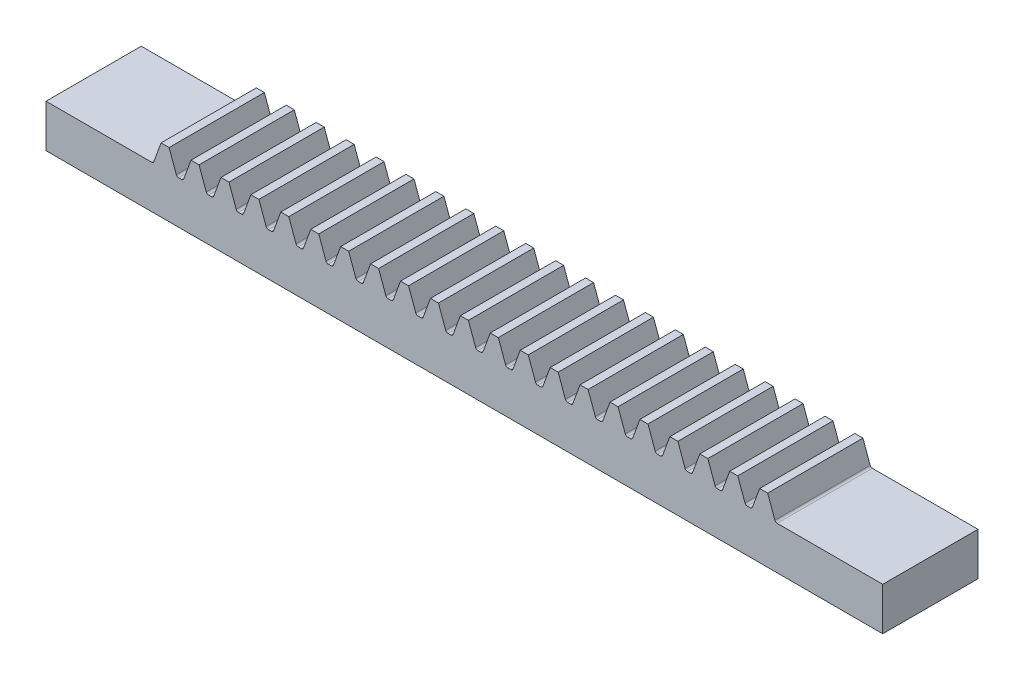
SolidWorks part; units mm, degrees
material "ABS"
ref_plane "Front Plane" through (0, 0, 0) normal (0, 0, 1) x (1, 0, 0)
ref_plane "Top Plane" through (0, 0, 0) normal (0, 1, 0) x (1, 0, 0)
ref_plane "Right Plane" through (0, 0, 0) normal (1, 0, 0) x (0, 0, -1)
sketch "Sketch1" plane through (0, 0, 0) normal (0, 0, 1) x (1, 0, 0)
  line L0 (5.5, 0) -> (-5.5, 0) construction
  line L1 (-77.8319, 4) -> (77.8319, 4)
  line L2 (-77.8319, 4) -> (-77.8319, 0)
  line L3 (-77.8319, 0) -> (77.8319, 0)
  line L4 (77.8319, 4) -> (77.8319, 0)
  line L5 (0, -9.2078) -> (0, 9.2078) construction
  dimension "D1" = 155.6637
  dimension "D2" = 77.8319
extrude "Boss-Extrude1" add sketch "Sketch1" along normal blind 10
sketch "Sketch2" plane through (0, 0, 0) normal (0, 0, 1) x (1, 0, 0)
  line L0 (-65.3126, 4) -> (-63.6747, 8.5)
  line L1 (77.8319, 4) -> (-77.8319, 4) construction
  line L2 (-63.6747, 8.5) -> (-61.989, 8.5)
  line L3 (-61.989, 8.5) -> (-60.3511, 4)
  line L4 (-65.3126, 4) -> (-60.3511, 4)
  line L5 (0, -9.2078) -> (0, 9.2078) construction
  line L6 (-62.8319, 8.5) -> (-62.8319, 4) construction
  line L9 (-34.7801, 6.5) -> (34.9733, 6.5) construction
  point P18 (-61.2611, 6.5)
  point P19 (-64.4026, 6.5)
  dimension "D2" = 20
  dimension "D3" = 40
  dimension "D4" = 62.8319
  dimension "D1" = 2.5
  dimension "D5" = 2
  dimension "D6" = 3.1416
extrude "Boss-Extrude4" add sketch "Sketch2" along normal up to surface (10 mm away) up to face at (0, 2, 10)
fillet "Fillet1" radius 0.5 2 edges
pattern_linear "LPattern1" count 21 spacing 6.2832 along (1, 0, 0) of "Boss-Extrude4", "Fillet1"
hole_wizard "CSK for M4 Hex Socket Countersunk Cap Screw1" [suppressed] positions "Sketch7" profile "Sketch6" countersink size "M4" standard "ISO"
sketch "Sketch7" plane through (0, 4, 0) normal (0, 1, 0) x (1, 0, 0)
  line L0 (-77.8319, -10) -> (-77.8319, 0) construction
  line L1 (77.8319, -10) -> (77.8319, 0) construction
  line L2 (-4.5728, 0) -> (4.5728, 0) construction
  point P0 (-71.8319, -5)
  point P2 (71.8319, -5)
  dimension "D1" = 6
  dimension "D2" = 6
  dimension "D3" = 5
  dimension "D4" = 5
sketch "Sketch6" plane through (-71.8319, 4, 5) normal (1, 0, 0) x (0, 0, 1)
  line L0 (0, 0) -> (0, 4)
  line L1 (0, 4) -> (2.25, 4)
  line L2 (2.25, 4) -> (2.25, 2.23)
  line L3 (2.25, 2.23) -> (4.48, 0)
  line L5 (4.48, 0) -> (0, 0)
  line L6 (-2.25, 2.23) -> (-4.48, 0) construction
  line L11 (0, -6.35) -> (0, 107.95) construction
  dimension "Thru Hole Dia." = 4.5
  dimension "Thru Hole Depth" = 4
  dimension "Near C'Sink Dia." = 8.96
  dimension "Near C'Sink Angle" = 90
ref_plane "Plane1" through (0, 26.5, 0) normal (0, 1, 0) x (1, 0, 0)
sketch "Sketch8" [suppressed] plane through (0, 0, 0) normal (0, -1, 0) x (1, 0, 0)
  line L4 (-77.8319, 0) -> (77.8319, 0)
  line L5 (77.8319, 0) -> (77.8319, 10)
  line L6 (77.8319, 10) -> (-77.8319, 10)
  line L7 (-77.8319, 10) -> (-77.8319, 0)
  line L8 (-77.8319, 0) -> (77.8319, 0)
  line L9 (77.8319, 0) -> (77.8319, 10)
  line L10 (77.8319, 10) -> (-77.8319, 10)
  line L11 (-77.8319, 10) -> (-77.8319, 0)
  circle A0 centre (-71.8319, 5) radius 2.25 construction
  circle A1 centre (-71.8319, 5) radius 2.25
  dimension "D1" = 0
extrude "Boss-Extrude5" [suppressed] add sketch "Sketch8" along normal blind 30
sketch "Sketch9" plane through (0, 0, 10) normal (0, 0, 1) x (1, 0, 0)
  line L88 (-77.8319, 4) -> (-77.8319, 0)
  line L89 (-77.8319, 0) -> (77.8319, 0)
  line L90 (-77.8319, 4) -> (-77.8319, 0)
  line L91 (77.8319, 4) -> (65.6627, 4)
  line L92 (65.1928, 4.329) -> (63.6747, 8.5)
  line L93 (63.6747, 8.5) -> (61.989, 8.5)
  line L94 (61.989, 8.5) -> (60.4709, 4.329)
  line L95 (60.001, 4) -> (59.3795, 4)
  line L96 (58.9096, 4.329) -> (57.3915, 8.5)
  line L97 (57.3915, 8.5) -> (55.7058, 8.5)
  line L98 (55.7058, 8.5) -> (54.1877, 4.329)
  line L99 (53.7178, 4) -> (53.0963, 4)
  line L100 (52.6265, 4.329) -> (51.1083, 8.5)
  line L101 (51.1083, 8.5) -> (49.4226, 8.5)
  line L102 (49.4226, 8.5) -> (47.9045, 4.329)
  line L103 (47.4347, 4) -> (46.8131, 4)
  line L104 (46.3433, 4.329) -> (44.8252, 8.5)
  line L105 (44.8252, 8.5) -> (43.1394, 8.5)
  line L106 (43.1394, 8.5) -> (41.6213, 4.329)
  line L107 (41.1515, 4) -> (40.5299, 4)
  line L108 (40.0601, 4.329) -> (38.542, 8.5)
  line L109 (38.542, 8.5) -> (36.8563, 8.5)
  line L110 (36.8563, 8.5) -> (35.3381, 4.329)
  line L111 (34.8683, 4) -> (34.2468, 4)
  line L112 (33.7769, 4.329) -> (32.2588, 8.5)
  line L113 (32.2588, 8.5) -> (30.5731, 8.5)
  line L114 (30.5731, 8.5) -> (29.0549, 4.329)
  line L115 (28.5851, 4) -> (27.9636, 4)
  line L116 (27.4937, 4.329) -> (25.9756, 8.5)
  line L117 (25.9756, 8.5) -> (24.2899, 8.5)
  line L118 (24.2899, 8.5) -> (22.7718, 4.329)
  line L119 (22.3019, 4) -> (21.6804, 4)
  line L120 (21.2105, 4.329) -> (19.6924, 8.5)
  line L121 (19.6924, 8.5) -> (18.0067, 8.5)
  line L122 (18.0067, 8.5) -> (16.4886, 4.329)
  line L123 (16.0187, 4) -> (15.3972, 4)
  line L124 (14.9273, 4.329) -> (13.4092, 8.5)
  line L125 (13.4092, 8.5) -> (11.7235, 8.5)
  line L126 (11.7235, 8.5) -> (10.2054, 4.329)
  line L127 (9.7355, 4) -> (9.114, 4)
  line L128 (8.6442, 4.329) -> (7.126, 8.5)
  line L129 (7.126, 8.5) -> (5.4403, 8.5)
  line L130 (5.4403, 8.5) -> (3.9222, 4.329)
  line L131 (3.4524, 4) -> (2.8308, 4)
  line L132 (2.361, 4.329) -> (0.8429, 8.5)
  line L133 (0.8429, 8.5) -> (-0.8429, 8.5)
  line L134 (-0.8429, 8.5) -> (-2.361, 4.329)
  line L135 (-2.8308, 4) -> (-3.4524, 4)
  line L136 (-3.9222, 4.329) -> (-5.4403, 8.5)
  line L137 (-5.4403, 8.5) -> (-7.126, 8.5)
  line L138 (-7.126, 8.5) -> (-8.6442, 4.329)
  line L139 (-9.114, 4) -> (-9.7355, 4)
  line L140 (-10.2054, 4.329) -> (-11.7235, 8.5)
  line L141 (-11.7235, 8.5) -> (-13.4092, 8.5)
  line L142 (-13.4092, 8.5) -> (-14.9273, 4.329)
  line L143 (-15.3972, 4) -> (-16.0187, 4)
  line L144 (-16.4886, 4.329) -> (-18.0067, 8.5)
  line L145 (-18.0067, 8.5) -> (-19.6924, 8.5)
  line L146 (-19.6924, 8.5) -> (-21.2105, 4.329)
  line L147 (-21.6804, 4) -> (-22.3019, 4)
  line L148 (-22.7718, 4.329) -> (-24.2899, 8.5)
  line L149 (-24.2899, 8.5) -> (-25.9756, 8.5)
  line L150 (-25.9756, 8.5) -> (-27.4937, 4.329)
  line L151 (-27.9636, 4) -> (-28.5851, 4)
  line L152 (-29.0549, 4.329) -> (-30.5731, 8.5)
  line L153 (-30.5731, 8.5) -> (-32.2588, 8.5)
  line L154 (-32.2588, 8.5) -> (-33.7769, 4.329)
  line L155 (-34.2468, 4) -> (-34.8683, 4)
  line L156 (-35.3381, 4.329) -> (-36.8563, 8.5)
  line L157 (-36.8563, 8.5) -> (-38.542, 8.5)
  line L158 (-38.542, 8.5) -> (-40.0601, 4.329)
  line L159 (-40.5299, 4) -> (-41.1515, 4)
  line L160 (-41.6213, 4.329) -> (-43.1394, 8.5)
  line L161 (-43.1394, 8.5) -> (-44.8252, 8.5)
  line L162 (-44.8252, 8.5) -> (-46.3433, 4.329)
  line L163 (-46.8131, 4) -> (-47.4347, 4)
  line L164 (-47.9045, 4.329) -> (-49.4226, 8.5)
  line L165 (-49.4226, 8.5) -> (-51.1083, 8.5)
  line L166 (-51.1083, 8.5) -> (-52.6265, 4.329)
  line L167 (-53.0963, 4) -> (-53.7178, 4)
  line L168 (-54.1877, 4.329) -> (-55.7058, 8.5)
  line L169 (-55.7058, 8.5) -> (-57.3915, 8.5)
  line L170 (-57.3915, 8.5) -> (-58.9096, 4.329)
  line L171 (-59.3795, 4) -> (-60.001, 4)
  line L172 (-60.4709, 4.329) -> (-61.989, 8.5)
  line L173 (-61.989, 8.5) -> (-63.6747, 8.5)
  line L174 (-63.6747, 8.5) -> (-65.1928, 4.329)
  line L175 (-65.6627, 4) -> (-77.8319, 4)
  line L176 (77.8319, 0) -> (77.8319, 4)
  line L177 (-77.8319, 0) -> (77.8319, 0)
  line L178 (77.8319, 0) -> (77.8319, 4)
  line L179 (77.8319, 4) -> (65.6627, 4)
  line L180 (65.1928, 4.329) -> (63.6747, 8.5)
  line L181 (63.6747, 8.5) -> (61.989, 8.5)
  line L182 (61.989, 8.5) -> (60.4709, 4.329)
  line L183 (60.001, 4) -> (59.3795, 4)
  line L184 (58.9096, 4.329) -> (57.3915, 8.5)
  line L185 (57.3915, 8.5) -> (55.7058, 8.5)
  line L186 (55.7058, 8.5) -> (54.1877, 4.329)
  line L187 (53.7178, 4) -> (53.0963, 4)
  line L188 (52.6265, 4.329) -> (51.1083, 8.5)
  line L189 (51.1083, 8.5) -> (49.4226, 8.5)
  line L190 (49.4226, 8.5) -> (47.9045, 4.329)
  line L191 (47.4347, 4) -> (46.8131, 4)
  line L192 (46.3433, 4.329) -> (44.8252, 8.5)
  line L193 (44.8252, 8.5) -> (43.1394, 8.5)
  line L194 (43.1394, 8.5) -> (41.6213, 4.329)
  line L195 (41.1515, 4) -> (40.5299, 4)
  line L196 (40.0601, 4.329) -> (38.542, 8.5)
  line L197 (38.542, 8.5) -> (36.8563, 8.5)
  line L198 (36.8563, 8.5) -> (35.3381, 4.329)
  line L199 (34.8683, 4) -> (34.2468, 4)
  line L200 (33.7769, 4.329) -> (32.2588, 8.5)
  line L201 (32.2588, 8.5) -> (30.5731, 8.5)
  line L202 (30.5731, 8.5) -> (29.0549, 4.329)
  line L203 (28.5851, 4) -> (27.9636, 4)
  line L204 (27.4937, 4.329) -> (25.9756, 8.5)
  line L205 (25.9756, 8.5) -> (24.2899, 8.5)
  line L206 (24.2899, 8.5) -> (22.7718, 4.329)
  line L207 (22.3019, 4) -> (21.6804, 4)
  line L208 (21.2105, 4.329) -> (19.6924, 8.5)
  line L209 (19.6924, 8.5) -> (18.0067, 8.5)
  line L210 (18.0067, 8.5) -> (16.4886, 4.329)
  line L211 (16.0187, 4) -> (15.3972, 4)
  line L212 (14.9273, 4.329) -> (13.4092, 8.5)
  line L213 (13.4092, 8.5) -> (11.7235, 8.5)
  line L214 (11.7235, 8.5) -> (10.2054, 4.329)
  line L215 (9.7355, 4) -> (9.114, 4)
  line L216 (8.6442, 4.329) -> (7.126, 8.5)
  line L217 (7.126, 8.5) -> (5.4403, 8.5)
  line L218 (5.4403, 8.5) -> (3.9222, 4.329)
  line L219 (3.4524, 4) -> (2.8308, 4)
  line L220 (2.361, 4.329) -> (0.8429, 8.5)
  line L221 (0.8429, 8.5) -> (-0.8429, 8.5)
  line L222 (-0.8429, 8.5) -> (-2.361, 4.329)
  line L223 (-2.8308, 4) -> (-3.4524, 4)
  line L224 (-3.9222, 4.329) -> (-5.4403, 8.5)
  line L225 (-5.4403, 8.5) -> (-7.126, 8.5)
  line L226 (-7.126, 8.5) -> (-8.6442, 4.329)
  line L227 (-9.114, 4) -> (-9.7355, 4)
  line L228 (-10.2054, 4.329) -> (-11.7235, 8.5)
  line L229 (-11.7235, 8.5) -> (-13.4092, 8.5)
  line L230 (-13.4092, 8.5) -> (-14.9273, 4.329)
  line L231 (-15.3972, 4) -> (-16.0187, 4)
  line L232 (-16.4886, 4.329) -> (-18.0067, 8.5)
  line L233 (-18.0067, 8.5) -> (-19.6924, 8.5)
  line L234 (-19.6924, 8.5) -> (-21.2105, 4.329)
  line L235 (-21.6804, 4) -> (-22.3019, 4)
  line L236 (-22.7718, 4.329) -> (-24.2899, 8.5)
  line L237 (-24.2899, 8.5) -> (-25.9756, 8.5)
  line L238 (-25.9756, 8.5) -> (-27.4937, 4.329)
  line L239 (-27.9636, 4) -> (-28.5851, 4)
  line L240 (-29.0549, 4.329) -> (-30.5731, 8.5)
  line L241 (-30.5731, 8.5) -> (-32.2588, 8.5)
  line L242 (-32.2588, 8.5) -> (-33.7769, 4.329)
  line L243 (-34.2468, 4) -> (-34.8683, 4)
  line L244 (-35.3381, 4.329) -> (-36.8563, 8.5)
  line L245 (-36.8563, 8.5) -> (-38.542, 8.5)
  line L246 (-38.542, 8.5) -> (-40.0601, 4.329)
  line L247 (-40.5299, 4) -> (-41.1515, 4)
  line L248 (-41.6213, 4.329) -> (-43.1394, 8.5)
  line L249 (-43.1394, 8.5) -> (-44.8252, 8.5)
  line L250 (-44.8252, 8.5) -> (-46.3433, 4.329)
  line L251 (-46.8131, 4) -> (-47.4347, 4)
  line L252 (-47.9045, 4.329) -> (-49.4226, 8.5)
  line L253 (-49.4226, 8.5) -> (-51.1083, 8.5)
  line L254 (-51.1083, 8.5) -> (-52.6265, 4.329)
  line L255 (-53.0963, 4) -> (-53.7178, 4)
  line L256 (-54.1877, 4.329) -> (-55.7058, 8.5)
  line L257 (-55.7058, 8.5) -> (-57.3915, 8.5)
  line L258 (-57.3915, 8.5) -> (-58.9096, 4.329)
  line L259 (-59.3795, 4) -> (-60.001, 4)
  line L260 (-60.4709, 4.329) -> (-61.989, 8.5)
  line L261 (-61.989, 8.5) -> (-63.6747, 8.5)
  line L262 (-63.6747, 8.5) -> (-65.1928, 4.329)
  line L263 (-65.6627, 4) -> (-77.8319, 4)
  arc A42 (65.1928, 4.329) -> (65.6627, 4) centre (65.6627, 4.5) ccw
  arc A43 (60.001, 4) -> (60.4709, 4.329) centre (60.001, 4.5) ccw
  arc A44 (58.9096, 4.329) -> (59.3795, 4) centre (59.3795, 4.5) ccw
  arc A45 (53.7178, 4) -> (54.1877, 4.329) centre (53.7178, 4.5) ccw
  arc A46 (52.6265, 4.329) -> (53.0963, 4) centre (53.0963, 4.5) ccw
  arc A47 (47.4347, 4) -> (47.9045, 4.329) centre (47.4347, 4.5) ccw
  arc A48 (46.3433, 4.329) -> (46.8131, 4) centre (46.8131, 4.5) ccw
  arc A49 (41.1515, 4) -> (41.6213, 4.329) centre (41.1515, 4.5) ccw
  arc A50 (40.0601, 4.329) -> (40.5299, 4) centre (40.5299, 4.5) ccw
  arc A51 (34.8683, 4) -> (35.3381, 4.329) centre (34.8683, 4.5) ccw
  arc A52 (33.7769, 4.329) -> (34.2468, 4) centre (34.2468, 4.5) ccw
  arc A53 (28.5851, 4) -> (29.0549, 4.329) centre (28.5851, 4.5) ccw
  arc A54 (27.4937, 4.329) -> (27.9636, 4) centre (27.9636, 4.5) ccw
  arc A55 (22.3019, 4) -> (22.7718, 4.329) centre (22.3019, 4.5) ccw
  arc A56 (21.2105, 4.329) -> (21.6804, 4) centre (21.6804, 4.5) ccw
  arc A57 (16.0187, 4) -> (16.4886, 4.329) centre (16.0187, 4.5) ccw
  arc A58 (14.9273, 4.329) -> (15.3972, 4) centre (15.3972, 4.5) ccw
  arc A59 (9.7355, 4) -> (10.2054, 4.329) centre (9.7355, 4.5) ccw
  arc A60 (8.6442, 4.329) -> (9.114, 4) centre (9.114, 4.5) ccw
  arc A61 (3.4524, 4) -> (3.9222, 4.329) centre (3.4524, 4.5) ccw
  arc A62 (2.361, 4.329) -> (2.8308, 4) centre (2.8308, 4.5) ccw
  arc A63 (-2.8308, 4) -> (-2.361, 4.329) centre (-2.8308, 4.5) ccw
  arc A64 (-3.9222, 4.329) -> (-3.4524, 4) centre (-3.4524, 4.5) ccw
  arc A65 (-9.114, 4) -> (-8.6442, 4.329) centre (-9.114, 4.5) ccw
  arc A66 (-10.2054, 4.329) -> (-9.7355, 4) centre (-9.7355, 4.5) ccw
  arc A67 (-15.3972, 4) -> (-14.9273, 4.329) centre (-15.3972, 4.5) ccw
  arc A68 (-16.4886, 4.329) -> (-16.0187, 4) centre (-16.0187, 4.5) ccw
  arc A69 (-21.6804, 4) -> (-21.2105, 4.329) centre (-21.6804, 4.5) ccw
  arc A70 (-22.7718, 4.329) -> (-22.3019, 4) centre (-22.3019, 4.5) ccw
  arc A71 (-27.9636, 4) -> (-27.4937, 4.329) centre (-27.9636, 4.5) ccw
  arc A72 (-29.0549, 4.329) -> (-28.5851, 4) centre (-28.5851, 4.5) ccw
  arc A73 (-34.2468, 4) -> (-33.7769, 4.329) centre (-34.2468, 4.5) ccw
  arc A74 (-35.3381, 4.329) -> (-34.8683, 4) centre (-34.8683, 4.5) ccw
  arc A75 (-40.5299, 4) -> (-40.0601, 4.329) centre (-40.5299, 4.5) ccw
  arc A76 (-41.6213, 4.329) -> (-41.1515, 4) centre (-41.1515, 4.5) ccw
  arc A77 (-46.8131, 4) -> (-46.3433, 4.329) centre (-46.8131, 4.5) ccw
  arc A78 (-47.9045, 4.329) -> (-47.4347, 4) centre (-47.4347, 4.5) ccw
  arc A79 (-53.0963, 4) -> (-52.6265, 4.329) centre (-53.0963, 4.5) ccw
  arc A80 (-54.1877, 4.329) -> (-53.7178, 4) centre (-53.7178, 4.5) ccw
  arc A81 (-59.3795, 4) -> (-58.9096, 4.329) centre (-59.3795, 4.5) ccw
  arc A82 (-60.4709, 4.329) -> (-60.001, 4) centre (-60.001, 4.5) ccw
  arc A83 (-65.6627, 4) -> (-65.1928, 4.329) centre (-65.6627, 4.5) ccw
  arc A84 (65.1928, 4.329) -> (65.6627, 4) centre (65.6627, 4.5) ccw
  arc A85 (60.001, 4) -> (60.4709, 4.329) centre (60.001, 4.5) ccw
  arc A86 (58.9096, 4.329) -> (59.3795, 4) centre (59.3795, 4.5) ccw
  arc A87 (53.7178, 4) -> (54.1877, 4.329) centre (53.7178, 4.5) ccw
  arc A88 (52.6265, 4.329) -> (53.0963, 4) centre (53.0963, 4.5) ccw
  arc A89 (47.4347, 4) -> (47.9045, 4.329) centre (47.4347, 4.5) ccw
  arc A90 (46.3433, 4.329) -> (46.8131, 4) centre (46.8131, 4.5) ccw
  arc A91 (41.1515, 4) -> (41.6213, 4.329) centre (41.1515, 4.5) ccw
  arc A92 (40.0601, 4.329) -> (40.5299, 4) centre (40.5299, 4.5) ccw
  arc A93 (34.8683, 4) -> (35.3381, 4.329) centre (34.8683, 4.5) ccw
  arc A94 (33.7769, 4.329) -> (34.2468, 4) centre (34.2468, 4.5) ccw
  arc A95 (28.5851, 4) -> (29.0549, 4.329) centre (28.5851, 4.5) ccw
  arc A96 (27.4937, 4.329) -> (27.9636, 4) centre (27.9636, 4.5) ccw
  arc A97 (22.3019, 4) -> (22.7718, 4.329) centre (22.3019, 4.5) ccw
  arc A98 (21.2105, 4.329) -> (21.6804, 4) centre (21.6804, 4.5) ccw
  arc A99 (16.0187, 4) -> (16.4886, 4.329) centre (16.0187, 4.5) ccw
  arc A100 (14.9273, 4.329) -> (15.3972, 4) centre (15.3972, 4.5) ccw
  arc A101 (9.7355, 4) -> (10.2054, 4.329) centre (9.7355, 4.5) ccw
  arc A102 (8.6442, 4.329) -> (9.114, 4) centre (9.114, 4.5) ccw
  arc A103 (3.4524, 4) -> (3.9222, 4.329) centre (3.4524, 4.5) ccw
  arc A104 (2.361, 4.329) -> (2.8308, 4) centre (2.8308, 4.5) ccw
  arc A105 (-2.8308, 4) -> (-2.361, 4.329) centre (-2.8308, 4.5) ccw
  arc A106 (-3.9222, 4.329) -> (-3.4524, 4) centre (-3.4524, 4.5) ccw
  arc A107 (-9.114, 4) -> (-8.6442, 4.329) centre (-9.114, 4.5) ccw
  arc A108 (-10.2054, 4.329) -> (-9.7355, 4) centre (-9.7355, 4.5) ccw
  arc A109 (-15.3972, 4) -> (-14.9273, 4.329) centre (-15.3972, 4.5) ccw
  arc A110 (-16.4886, 4.329) -> (-16.0187, 4) centre (-16.0187, 4.5) ccw
  arc A111 (-21.6804, 4) -> (-21.2105, 4.329) centre (-21.6804, 4.5) ccw
  arc A112 (-22.7718, 4.329) -> (-22.3019, 4) centre (-22.3019, 4.5) ccw
  arc A113 (-27.9636, 4) -> (-27.4937, 4.329) centre (-27.9636, 4.5) ccw
  arc A114 (-29.0549, 4.329) -> (-28.5851, 4) centre (-28.5851, 4.5) ccw
  arc A115 (-34.2468, 4) -> (-33.7769, 4.329) centre (-34.2468, 4.5) ccw
  arc A116 (-35.3381, 4.329) -> (-34.8683, 4) centre (-34.8683, 4.5) ccw
  arc A117 (-40.5299, 4) -> (-40.0601, 4.329) centre (-40.5299, 4.5) ccw
  arc A118 (-41.6213, 4.329) -> (-41.1515, 4) centre (-41.1515, 4.5) ccw
  arc A119 (-46.8131, 4) -> (-46.3433, 4.329) centre (-46.8131, 4.5) ccw
  arc A120 (-47.9045, 4.329) -> (-47.4347, 4) centre (-47.4347, 4.5) ccw
  arc A121 (-53.0963, 4) -> (-52.6265, 4.329) centre (-53.0963, 4.5) ccw
  arc A122 (-54.1877, 4.329) -> (-53.7178, 4) centre (-53.7178, 4.5) ccw
  arc A123 (-59.3795, 4) -> (-58.9096, 4.329) centre (-59.3795, 4.5) ccw
  arc A124 (-60.4709, 4.329) -> (-60.001, 4) centre (-60.001, 4.5) ccw
  arc A125 (-65.6627, 4) -> (-65.1928, 4.329) centre (-65.6627, 4.5) ccw
  dimension "D1" = 0
extrude "Boss-Extrude6" add sketch "Sketch9" along normal blind 6 contours L262 A125 L263 L90 L177 L178 L179 A84 L180 L181 L182 A85 L183 A86 L184 L185 L186 A87 L187 A88 L188 L189 L190 A89 L191 A90 L192 L193 L194 A91 L195 A92 L196 L197 L198 A93 L199 A94 L200 L201 L202 A95 L203 A96 L204 L205 L206 A97 L207 A98 L208 L209 L210 A99 L211 A100 L212 L213 L214 A101 L215 A102 L216 L217 L218 A103 L219 A104 L220 L221 L222 A105 L223 A106 L224 L225 L226 A107 L227 A108 L228 L229 L230 A109 L231 A110 L232 L233 L234 A111 L235 A112 L236 L237 L238 A113 L239 A114 L240 L241 L242 A115 L243 A116 L244 L245 L246 A117 L247 A118 L248 L249 L250 A119 L251 A120 L252 L253 L254 A121 L255 A122 L256 L257 L258 A123 L259 A124 L260 L261
sketch "Sketch10" [suppressed] plane through (0, 0, 16) normal (0, 0, 1) x (1, 0, 0)
  line L0 (-49.4226, 8.5) -> (-51.1083, 8.5) construction
  line L1 (-77.8319, -30) -> (90.1846, -30)
  line L2 (-77.8319, -30) -> (-77.8319, -7.5)
  line L3 (-77.8319, -7.5) -> (90.1846, -7.5)
  line L4 (90.1846, -30) -> (90.1846, -7.5)
  dimension "D1" = 16
extrude "Cut-Extrude1" [suppressed] cut sketch "Sketch10" against normal blind 40
sketch "Sketch11" plane through (-77.8319, 0, 0) normal (-1, 0, 0) x (0, 0, 1)
  line L4 (0, 4) -> (0, 0)
  line L5 (0, 0) -> (16, 0)
  line L6 (16, 0) -> (16, 4)
  line L7 (16, 4) -> (0, 4)
  line L8 (0, 4) -> (0, 0)
  line L9 (0, 0) -> (16, 0)
  line L10 (16, 0) -> (16, 4)
  line L11 (16, 4) -> (0, 4)
  dimension "D1" = 0
extrude "Boss-Extrude8" add sketch "Sketch11" along normal blind 10
sketch "Sketch12" plane through (77.8319, 0, 0) normal (1, 0, 0) x (0, 0, -1)
  line L4 (-16, 4) -> (-16, 0)
  line L5 (-16, 0) -> (0, 0)
  line L6 (0, 0) -> (0, 4)
  line L7 (0, 4) -> (-16, 4)
  line L8 (-16, 4) -> (-16, 0)
  line L9 (-16, 0) -> (0, 0)
  line L10 (0, 0) -> (0, 4)
  line L11 (0, 4) -> (-16, 4)
  dimension "D1" = 0
extrude "Boss-Extrude9" add sketch "Sketch12" along normal blind 10
sketch "Sketch15" plane through (0, 0, 0) normal (0, -1, 0) x (1, 0, 0)
  line L4 (-87.8319, 0) -> (87.8319, 0)
  line L5 (87.8319, 0) -> (87.8319, 16)
  line L6 (87.8319, 16) -> (-87.8319, 16)
  line L7 (-87.8319, 16) -> (-87.8319, 0)
  line L8 (-87.8319, 0) -> (87.8319, 0)
  line L9 (87.8319, 0) -> (87.8319, 16)
  line L10 (87.8319, 16) -> (-87.8319, 16)
  line L11 (-87.8319, 16) -> (-87.8319, 0)
  dimension "D1" = 0
extrude "Boss-Extrude10" add sketch "Sketch15" along normal blind 5
sketch "Sketch16" plane through (0, 0, 16) normal (0, 0, 1) x (1, 0, 0)
  line L88 (-61.989, 8.5) -> (-63.6747, 8.5)
  line L89 (-63.6747, 8.5) -> (-65.1928, 4.329)
  line L90 (-65.6627, 4) -> (-87.8319, 4)
  line L91 (-87.8319, 4) -> (-87.8319, -5)
  line L92 (-87.8319, -5) -> (87.8319, -5)
  line L93 (87.8319, -5) -> (87.8319, 4)
  line L94 (87.8319, 4) -> (65.6627, 4)
  line L95 (65.1928, 4.329) -> (63.6747, 8.5)
  line L96 (63.6747, 8.5) -> (61.989, 8.5)
  line L97 (61.989, 8.5) -> (60.4709, 4.329)
  line L98 (60.001, 4) -> (59.3795, 4)
  line L99 (58.9096, 4.329) -> (57.3915, 8.5)
  line L100 (57.3915, 8.5) -> (55.7058, 8.5)
  line L101 (55.7058, 8.5) -> (54.1877, 4.329)
  line L102 (53.7178, 4) -> (53.0963, 4)
  line L103 (52.6265, 4.329) -> (51.1083, 8.5)
  line L104 (51.1083, 8.5) -> (49.4226, 8.5)
  line L105 (49.4226, 8.5) -> (47.9045, 4.329)
  line L106 (47.4347, 4) -> (46.8131, 4)
  line L107 (46.3433, 4.329) -> (44.8252, 8.5)
  line L108 (44.8252, 8.5) -> (43.1394, 8.5)
  line L109 (43.1394, 8.5) -> (41.6213, 4.329)
  line L110 (41.1515, 4) -> (40.5299, 4)
  line L111 (40.0601, 4.329) -> (38.542, 8.5)
  line L112 (38.542, 8.5) -> (36.8563, 8.5)
  line L113 (36.8563, 8.5) -> (35.3381, 4.329)
  line L114 (34.8683, 4) -> (34.2468, 4)
  line L115 (33.7769, 4.329) -> (32.2588, 8.5)
  line L116 (32.2588, 8.5) -> (30.5731, 8.5)
  line L117 (30.5731, 8.5) -> (29.0549, 4.329)
  line L118 (28.5851, 4) -> (27.9636, 4)
  line L119 (27.4937, 4.329) -> (25.9756, 8.5)
  line L120 (25.9756, 8.5) -> (24.2899, 8.5)
  line L121 (24.2899, 8.5) -> (22.7718, 4.329)
  line L122 (22.3019, 4) -> (21.6804, 4)
  line L123 (21.2105, 4.329) -> (19.6924, 8.5)
  line L124 (19.6924, 8.5) -> (18.0067, 8.5)
  line L125 (18.0067, 8.5) -> (16.4886, 4.329)
  line L126 (16.0187, 4) -> (15.3972, 4)
  line L127 (14.9273, 4.329) -> (13.4092, 8.5)
  line L128 (13.4092, 8.5) -> (11.7235, 8.5)
  line L129 (11.7235, 8.5) -> (10.2054, 4.329)
  line L130 (9.7355, 4) -> (9.114, 4)
  line L131 (8.6442, 4.329) -> (7.126, 8.5)
  line L132 (7.126, 8.5) -> (5.4403, 8.5)
  line L133 (5.4403, 8.5) -> (3.9222, 4.329)
  line L134 (3.4524, 4) -> (2.8308, 4)
  line L135 (2.361, 4.329) -> (0.8429, 8.5)
  line L136 (0.8429, 8.5) -> (-0.8429, 8.5)
  line L137 (-0.8429, 8.5) -> (-2.361, 4.329)
  line L138 (-2.8308, 4) -> (-3.4524, 4)
  line L139 (-3.9222, 4.329) -> (-5.4403, 8.5)
  line L140 (-5.4403, 8.5) -> (-7.126, 8.5)
  line L141 (-7.126, 8.5) -> (-8.6442, 4.329)
  line L142 (-9.114, 4) -> (-9.7355, 4)
  line L143 (-10.2054, 4.329) -> (-11.7235, 8.5)
  line L144 (-11.7235, 8.5) -> (-13.4092, 8.5)
  line L145 (-13.4092, 8.5) -> (-14.9273, 4.329)
  line L146 (-15.3972, 4) -> (-16.0187, 4)
  line L147 (-16.4886, 4.329) -> (-18.0067, 8.5)
  line L148 (-18.0067, 8.5) -> (-19.6924, 8.5)
  line L149 (-19.6924, 8.5) -> (-21.2105, 4.329)
  line L150 (-21.6804, 4) -> (-22.3019, 4)
  line L151 (-22.7718, 4.329) -> (-24.2899, 8.5)
  line L152 (-24.2899, 8.5) -> (-25.9756, 8.5)
  line L153 (-25.9756, 8.5) -> (-27.4937, 4.329)
  line L154 (-27.9636, 4) -> (-28.5851, 4)
  line L155 (-29.0549, 4.329) -> (-30.5731, 8.5)
  line L156 (-30.5731, 8.5) -> (-32.2588, 8.5)
  line L157 (-32.2588, 8.5) -> (-33.7769, 4.329)
  line L158 (-34.2468, 4) -> (-34.8683, 4)
  line L159 (-35.3381, 4.329) -> (-36.8563, 8.5)
  line L160 (-36.8563, 8.5) -> (-38.542, 8.5)
  line L161 (-38.542, 8.5) -> (-40.0601, 4.329)
  line L162 (-40.5299, 4) -> (-41.1515, 4)
  line L163 (-41.6213, 4.329) -> (-43.1394, 8.5)
  line L164 (-43.1394, 8.5) -> (-44.8252, 8.5)
  line L165 (-44.8252, 8.5) -> (-46.3433, 4.329)
  line L166 (-46.8131, 4) -> (-47.4347, 4)
  line L167 (-47.9045, 4.329) -> (-49.4226, 8.5)
  line L168 (-49.4226, 8.5) -> (-51.1083, 8.5)
  line L169 (-51.1083, 8.5) -> (-52.6265, 4.329)
  line L170 (-53.0963, 4) -> (-53.7178, 4)
  line L171 (-54.1877, 4.329) -> (-55.7058, 8.5)
  line L172 (-55.7058, 8.5) -> (-57.3915, 8.5)
  line L173 (-57.3915, 8.5) -> (-58.9096, 4.329)
  line L174 (-59.3795, 4) -> (-60.001, 4)
  line L175 (-60.4709, 4.329) -> (-61.989, 8.5)
  line L176 (-61.989, 8.5) -> (-63.6747, 8.5)
  line L177 (-63.6747, 8.5) -> (-65.1928, 4.329)
  line L178 (-65.6627, 4) -> (-87.8319, 4)
  line L179 (-87.8319, 4) -> (-87.8319, -5)
  line L180 (-87.8319, -5) -> (87.8319, -5)
  line L181 (87.8319, -5) -> (87.8319, 4)
  line L182 (87.8319, 4) -> (65.6627, 4)
  line L183 (65.1928, 4.329) -> (63.6747, 8.5)
  line L184 (63.6747, 8.5) -> (61.989, 8.5)
  line L185 (61.989, 8.5) -> (60.4709, 4.329)
  line L186 (60.001, 4) -> (59.3795, 4)
  line L187 (58.9096, 4.329) -> (57.3915, 8.5)
  line L188 (57.3915, 8.5) -> (55.7058, 8.5)
  line L189 (55.7058, 8.5) -> (54.1877, 4.329)
  line L190 (53.7178, 4) -> (53.0963, 4)
  line L191 (52.6265, 4.329) -> (51.1083, 8.5)
  line L192 (51.1083, 8.5) -> (49.4226, 8.5)
  line L193 (49.4226, 8.5) -> (47.9045, 4.329)
  line L194 (47.4347, 4) -> (46.8131, 4)
  line L195 (46.3433, 4.329) -> (44.8252, 8.5)
  line L196 (44.8252, 8.5) -> (43.1394, 8.5)
  line L197 (43.1394, 8.5) -> (41.6213, 4.329)
  line L198 (41.1515, 4) -> (40.5299, 4)
  line L199 (40.0601, 4.329) -> (38.542, 8.5)
  line L200 (38.542, 8.5) -> (36.8563, 8.5)
  line L201 (36.8563, 8.5) -> (35.3381, 4.329)
  line L202 (34.8683, 4) -> (34.2468, 4)
  line L203 (33.7769, 4.329) -> (32.2588, 8.5)
  line L204 (32.2588, 8.5) -> (30.5731, 8.5)
  line L205 (30.5731, 8.5) -> (29.0549, 4.329)
  line L206 (28.5851, 4) -> (27.9636, 4)
  line L207 (27.4937, 4.329) -> (25.9756, 8.5)
  line L208 (25.9756, 8.5) -> (24.2899, 8.5)
  line L209 (24.2899, 8.5) -> (22.7718, 4.329)
  line L210 (22.3019, 4) -> (21.6804, 4)
  line L211 (21.2105, 4.329) -> (19.6924, 8.5)
  line L212 (19.6924, 8.5) -> (18.0067, 8.5)
  line L213 (18.0067, 8.5) -> (16.4886, 4.329)
  line L214 (16.0187, 4) -> (15.3972, 4)
  line L215 (14.9273, 4.329) -> (13.4092, 8.5)
  line L216 (13.4092, 8.5) -> (11.7235, 8.5)
  line L217 (11.7235, 8.5) -> (10.2054, 4.329)
  line L218 (9.7355, 4) -> (9.114, 4)
  line L219 (8.6442, 4.329) -> (7.126, 8.5)
  line L220 (7.126, 8.5) -> (5.4403, 8.5)
  line L221 (5.4403, 8.5) -> (3.9222, 4.329)
  line L222 (3.4524, 4) -> (2.8308, 4)
  line L223 (2.361, 4.329) -> (0.8429, 8.5)
  line L224 (0.8429, 8.5) -> (-0.8429, 8.5)
  line L225 (-0.8429, 8.5) -> (-2.361, 4.329)
  line L226 (-2.8308, 4) -> (-3.4524, 4)
  line L227 (-3.9222, 4.329) -> (-5.4403, 8.5)
  line L228 (-5.4403, 8.5) -> (-7.126, 8.5)
  line L229 (-7.126, 8.5) -> (-8.6442, 4.329)
  line L230 (-9.114, 4) -> (-9.7355, 4)
  line L231 (-10.2054, 4.329) -> (-11.7235, 8.5)
  line L232 (-11.7235, 8.5) -> (-13.4092, 8.5)
  line L233 (-13.4092, 8.5) -> (-14.9273, 4.329)
  line L234 (-15.3972, 4) -> (-16.0187, 4)
  line L235 (-16.4886, 4.329) -> (-18.0067, 8.5)
  line L236 (-18.0067, 8.5) -> (-19.6924, 8.5)
  line L237 (-19.6924, 8.5) -> (-21.2105, 4.329)
  line L238 (-21.6804, 4) -> (-22.3019, 4)
  line L239 (-22.7718, 4.329) -> (-24.2899, 8.5)
  line L240 (-24.2899, 8.5) -> (-25.9756, 8.5)
  line L241 (-25.9756, 8.5) -> (-27.4937, 4.329)
  line L242 (-27.9636, 4) -> (-28.5851, 4)
  line L243 (-29.0549, 4.329) -> (-30.5731, 8.5)
  line L244 (-30.5731, 8.5) -> (-32.2588, 8.5)
  line L245 (-32.2588, 8.5) -> (-33.7769, 4.329)
  line L246 (-34.2468, 4) -> (-34.8683, 4)
  line L247 (-35.3381, 4.329) -> (-36.8563, 8.5)
  line L248 (-36.8563, 8.5) -> (-38.542, 8.5)
  line L249 (-38.542, 8.5) -> (-40.0601, 4.329)
  line L250 (-40.5299, 4) -> (-41.1515, 4)
  line L251 (-41.6213, 4.329) -> (-43.1394, 8.5)
  line L252 (-43.1394, 8.5) -> (-44.8252, 8.5)
  line L253 (-44.8252, 8.5) -> (-46.3433, 4.329)
  line L254 (-46.8131, 4) -> (-47.4347, 4)
  line L255 (-47.9045, 4.329) -> (-49.4226, 8.5)
  line L256 (-49.4226, 8.5) -> (-51.1083, 8.5)
  line L257 (-51.1083, 8.5) -> (-52.6265, 4.329)
  line L258 (-53.0963, 4) -> (-53.7178, 4)
  line L259 (-54.1877, 4.329) -> (-55.7058, 8.5)
  line L260 (-55.7058, 8.5) -> (-57.3915, 8.5)
  line L261 (-57.3915, 8.5) -> (-58.9096, 4.329)
  line L262 (-59.3795, 4) -> (-60.001, 4)
  line L263 (-60.4709, 4.329) -> (-61.989, 8.5)
  arc A42 (-65.6627, 4) -> (-65.1928, 4.329) centre (-65.6627, 4.5) ccw
  arc A43 (65.1928, 4.329) -> (65.6627, 4) centre (65.6627, 4.5) ccw
  arc A44 (60.001, 4) -> (60.4709, 4.329) centre (60.001, 4.5) ccw
  arc A45 (58.9096, 4.329) -> (59.3795, 4) centre (59.3795, 4.5) ccw
  arc A46 (53.7178, 4) -> (54.1877, 4.329) centre (53.7178, 4.5) ccw
  arc A47 (52.6265, 4.329) -> (53.0963, 4) centre (53.0963, 4.5) ccw
  arc A48 (47.4347, 4) -> (47.9045, 4.329) centre (47.4347, 4.5) ccw
  arc A49 (46.3433, 4.329) -> (46.8131, 4) centre (46.8131, 4.5) ccw
  arc A50 (41.1515, 4) -> (41.6213, 4.329) centre (41.1515, 4.5) ccw
  arc A51 (40.0601, 4.329) -> (40.5299, 4) centre (40.5299, 4.5) ccw
  arc A52 (34.8683, 4) -> (35.3381, 4.329) centre (34.8683, 4.5) ccw
  arc A53 (33.7769, 4.329) -> (34.2468, 4) centre (34.2468, 4.5) ccw
  arc A54 (28.5851, 4) -> (29.0549, 4.329) centre (28.5851, 4.5) ccw
  arc A55 (27.4937, 4.329) -> (27.9636, 4) centre (27.9636, 4.5) ccw
  arc A56 (22.3019, 4) -> (22.7718, 4.329) centre (22.3019, 4.5) ccw
  arc A57 (21.2105, 4.329) -> (21.6804, 4) centre (21.6804, 4.5) ccw
  arc A58 (16.0187, 4) -> (16.4886, 4.329) centre (16.0187, 4.5) ccw
  arc A59 (14.9273, 4.329) -> (15.3972, 4) centre (15.3972, 4.5) ccw
  arc A60 (9.7355, 4) -> (10.2054, 4.329) centre (9.7355, 4.5) ccw
  arc A61 (8.6442, 4.329) -> (9.114, 4) centre (9.114, 4.5) ccw
  arc A62 (3.4524, 4) -> (3.9222, 4.329) centre (3.4524, 4.5) ccw
  arc A63 (2.361, 4.329) -> (2.8308, 4) centre (2.8308, 4.5) ccw
  arc A64 (-2.8308, 4) -> (-2.361, 4.329) centre (-2.8308, 4.5) ccw
  arc A65 (-3.9222, 4.329) -> (-3.4524, 4) centre (-3.4524, 4.5) ccw
  arc A66 (-9.114, 4) -> (-8.6442, 4.329) centre (-9.114, 4.5) ccw
  arc A67 (-10.2054, 4.329) -> (-9.7355, 4) centre (-9.7355, 4.5) ccw
  arc A68 (-15.3972, 4) -> (-14.9273, 4.329) centre (-15.3972, 4.5) ccw
  arc A69 (-16.4886, 4.329) -> (-16.0187, 4) centre (-16.0187, 4.5) ccw
  arc A70 (-21.6804, 4) -> (-21.2105, 4.329) centre (-21.6804, 4.5) ccw
  arc A71 (-22.7718, 4.329) -> (-22.3019, 4) centre (-22.3019, 4.5) ccw
  arc A72 (-27.9636, 4) -> (-27.4937, 4.329) centre (-27.9636, 4.5) ccw
  arc A73 (-29.0549, 4.329) -> (-28.5851, 4) centre (-28.5851, 4.5) ccw
  arc A74 (-34.2468, 4) -> (-33.7769, 4.329) centre (-34.2468, 4.5) ccw
  arc A75 (-35.3381, 4.329) -> (-34.8683, 4) centre (-34.8683, 4.5) ccw
  arc A76 (-40.5299, 4) -> (-40.0601, 4.329) centre (-40.5299, 4.5) ccw
  arc A77 (-41.6213, 4.329) -> (-41.1515, 4) centre (-41.1515, 4.5) ccw
  arc A78 (-46.8131, 4) -> (-46.3433, 4.329) centre (-46.8131, 4.5) ccw
  arc A79 (-47.9045, 4.329) -> (-47.4347, 4) centre (-47.4347, 4.5) ccw
  arc A80 (-53.0963, 4) -> (-52.6265, 4.329) centre (-53.0963, 4.5) ccw
  arc A81 (-54.1877, 4.329) -> (-53.7178, 4) centre (-53.7178, 4.5) ccw
  arc A82 (-59.3795, 4) -> (-58.9096, 4.329) centre (-59.3795, 4.5) ccw
  arc A83 (-60.4709, 4.329) -> (-60.001, 4) centre (-60.001, 4.5) ccw
  arc A84 (-65.6627, 4) -> (-65.1928, 4.329) centre (-65.6627, 4.5) ccw
  arc A85 (65.1928, 4.329) -> (65.6627, 4) centre (65.6627, 4.5) ccw
  arc A86 (60.001, 4) -> (60.4709, 4.329) centre (60.001, 4.5) ccw
  arc A87 (58.9096, 4.329) -> (59.3795, 4) centre (59.3795, 4.5) ccw
  arc A88 (53.7178, 4) -> (54.1877, 4.329) centre (53.7178, 4.5) ccw
  arc A89 (52.6265, 4.329) -> (53.0963, 4) centre (53.0963, 4.5) ccw
  arc A90 (47.4347, 4) -> (47.9045, 4.329) centre (47.4347, 4.5) ccw
  arc A91 (46.3433, 4.329) -> (46.8131, 4) centre (46.8131, 4.5) ccw
  arc A92 (41.1515, 4) -> (41.6213, 4.329) centre (41.1515, 4.5) ccw
  arc A93 (40.0601, 4.329) -> (40.5299, 4) centre (40.5299, 4.5) ccw
  arc A94 (34.8683, 4) -> (35.3381, 4.329) centre (34.8683, 4.5) ccw
  arc A95 (33.7769, 4.329) -> (34.2468, 4) centre (34.2468, 4.5) ccw
  arc A96 (28.5851, 4) -> (29.0549, 4.329) centre (28.5851, 4.5) ccw
  arc A97 (27.4937, 4.329) -> (27.9636, 4) centre (27.9636, 4.5) ccw
  arc A98 (22.3019, 4) -> (22.7718, 4.329) centre (22.3019, 4.5) ccw
  arc A99 (21.2105, 4.329) -> (21.6804, 4) centre (21.6804, 4.5) ccw
  arc A100 (16.0187, 4) -> (16.4886, 4.329) centre (16.0187, 4.5) ccw
  arc A101 (14.9273, 4.329) -> (15.3972, 4) centre (15.3972, 4.5) ccw
  arc A102 (9.7355, 4) -> (10.2054, 4.329) centre (9.7355, 4.5) ccw
  arc A103 (8.6442, 4.329) -> (9.114, 4) centre (9.114, 4.5) ccw
  arc A104 (3.4524, 4) -> (3.9222, 4.329) centre (3.4524, 4.5) ccw
  arc A105 (2.361, 4.329) -> (2.8308, 4) centre (2.8308, 4.5) ccw
  arc A106 (-2.8308, 4) -> (-2.361, 4.329) centre (-2.8308, 4.5) ccw
  arc A107 (-3.9222, 4.329) -> (-3.4524, 4) centre (-3.4524, 4.5) ccw
  arc A108 (-9.114, 4) -> (-8.6442, 4.329) centre (-9.114, 4.5) ccw
  arc A109 (-10.2054, 4.329) -> (-9.7355, 4) centre (-9.7355, 4.5) ccw
  arc A110 (-15.3972, 4) -> (-14.9273, 4.329) centre (-15.3972, 4.5) ccw
  arc A111 (-16.4886, 4.329) -> (-16.0187, 4) centre (-16.0187, 4.5) ccw
  arc A112 (-21.6804, 4) -> (-21.2105, 4.329) centre (-21.6804, 4.5) ccw
  arc A113 (-22.7718, 4.329) -> (-22.3019, 4) centre (-22.3019, 4.5) ccw
  arc A114 (-27.9636, 4) -> (-27.4937, 4.329) centre (-27.9636, 4.5) ccw
  arc A115 (-29.0549, 4.329) -> (-28.5851, 4) centre (-28.5851, 4.5) ccw
  arc A116 (-34.2468, 4) -> (-33.7769, 4.329) centre (-34.2468, 4.5) ccw
  arc A117 (-35.3381, 4.329) -> (-34.8683, 4) centre (-34.8683, 4.5) ccw
  arc A118 (-40.5299, 4) -> (-40.0601, 4.329) centre (-40.5299, 4.5) ccw
  arc A119 (-41.6213, 4.329) -> (-41.1515, 4) centre (-41.1515, 4.5) ccw
  arc A120 (-46.8131, 4) -> (-46.3433, 4.329) centre (-46.8131, 4.5) ccw
  arc A121 (-47.9045, 4.329) -> (-47.4347, 4) centre (-47.4347, 4.5) ccw
  arc A122 (-53.0963, 4) -> (-52.6265, 4.329) centre (-53.0963, 4.5) ccw
  arc A123 (-54.1877, 4.329) -> (-53.7178, 4) centre (-53.7178, 4.5) ccw
  arc A124 (-59.3795, 4) -> (-58.9096, 4.329) centre (-59.3795, 4.5) ccw
  arc A125 (-60.4709, 4.329) -> (-60.001, 4) centre (-60.001, 4.5) ccw
  dimension "D1" = 0
extrude "Boss-Extrude11" add sketch "Sketch16" along normal blind 4
equation "\"D1@Sketch1\"=((\"module\"*\"teeth\")*pi)+30"
equation "\"D2@Sketch1\"=\"D1@Sketch1\"/2"
equation "\"D3@Sketch1\"=\"module\"*2"
equation "\"D1@Boss-Extrude1\"=\"width\""
equation "\"D2@Sketch2\"=\"pressure\""
equation "\"D3@Sketch2\"=\"pressure\"*2"
equation "\"D4@Sketch2\"=((\"module\"*\"teeth\")/2)*pi"
equation "\"D1@Sketch2\"=\"module\"*1.25"
equation "\"D5@Sketch2\"=\"module\""
equation "\"D6@Sketch2\"=(pi/2)*\"module\""
equation "\"D3@LPattern1\"=\"module\"*pi"
equation "\"D1@LPattern1\"=\"teeth\"+1"
equation "\"D1@Sketch7\"=\"module\"*3"
equation "\"D2@Sketch7\"=\"module\"*3"
equation "\"D3@Sketch7\"=\"width\"/2"
equation "\"D4@Sketch7\"=\"width\"/2"
equation "\"D1@Plane1\"=(1.25*\"module\")+((\"module\"*\"teeth\")/2)"
